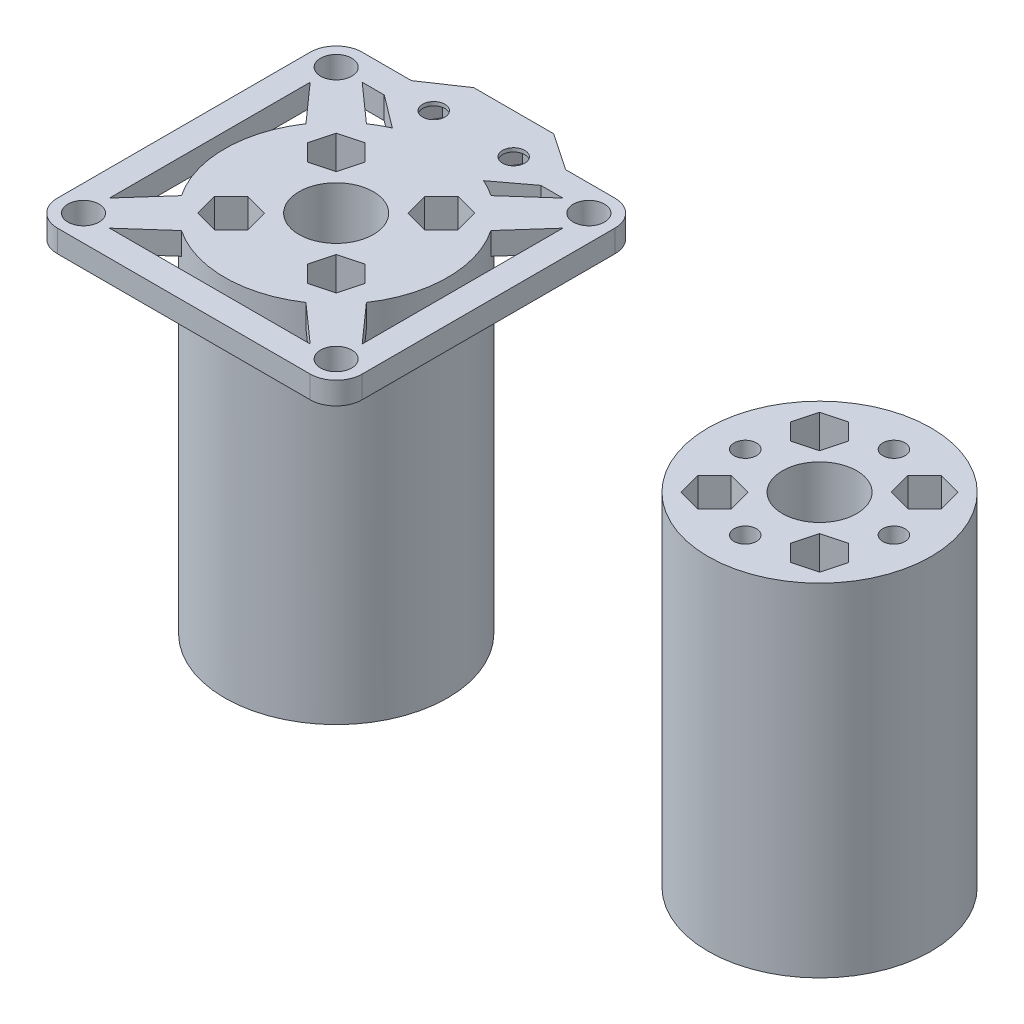
SolidWorks part; units mm, degrees
ref_plane "前视基准面" through (0, 0, 0) normal (0, 0, 1) x (1, 0, 0)
ref_plane "上视基准面" through (0, 0, 0) normal (0, 1, 0) x (1, 0, 0)
ref_plane "右视基准面" through (0, 0, 0) normal (1, 0, 0) x (0, 0, -1)
sketch "草图1" plane through (0, 0, 0) normal (0, 1, 0) x (1, 0, 0)
  circle A0 centre (-5.3729, -8.9317) radius 15
  circle A1 centre (-22.3729, 8.0683) radius 2.1
  circle A5 centre (-5.3729, -8.9317) radius 5
  circle A6 centre (-22.3729, 8.0683) radius 3.5
  dimension "D4" = 4.2
  dimension "D8" = 10
  dimension "D9" = 7
extrude "凸台-拉伸4" add sketch "草图1" along normal blind 3
sketch "草图5" plane through (0, 0, 0) normal (0, 1, 0) x (1, 0, 0)
  line L0 (-22.3729, 4.5683) -> (-10.3729, -8.9317)
  line L1 (-5.3729, -3.9317) -> (-18.8729, 8.0683)
  line L2 (-18.8729, 8.0683) -> (-22.3729, 4.5683)
  line L3 (-10.3729, -8.9317) -> (-10.3729, -3.9317)
  line L4 (-10.3729, -3.9317) -> (-5.3729, -3.9317)
  circle A0 centre (-22.3729, 8.0683) radius 3.5 construction
  circle A1 centre (-5.3729, -8.9317) radius 5 construction
extrude "凸台-拉伸5" add sketch "草图5" along normal blind 3
pattern_circular "阵列(圆周)2" count 4 over 360 about axis through (-5.3729, 0, 8.9317) along (0, 1, 0) of "凸台-拉伸5"
sketch "草图6" plane through (0, 3, 0) normal (0, 1, 0) x (1, 0, 0)
  circle A0 centre (11.6271, 8.0683) radius 2.1
  circle A1 centre (11.6271, 8.0683) radius 3.5
  dimension "D2" = 4.2
  dimension "D3" = 7
extrude "凸台-拉伸6" add sketch "草图6" against normal blind 3
pattern_circular "阵列(圆周)3" count 4 over 360 about axis through (-5.3729, 0, 8.9317) along (0, 1, 0) of "凸台-拉伸6"
sketch "草图7" plane through (0, 0, 0) normal (0, -1, 0) x (1, 0, 0)
  circle A0 centre (-5.3729, 8.9317) radius 15
  circle A1 centre (-5.3729, 8.9317) radius 5
extrude "凸台-拉伸7" add sketch "草图7" along normal blind 46
sketch "草图8" plane through (0, -46, 0) normal (0, -1, 0) x (1, 0, 0)
  line L4 (3.9435, 18.2482) -> (0.8763, 19.07)
  line L5 (0.8763, 19.07) -> (-1.3691, 16.8247)
  line L6 (-1.3691, 16.8247) -> (-0.5472, 13.7574)
  line L7 (-0.5472, 13.7574) -> (2.52, 12.9356)
  line L8 (2.52, 12.9356) -> (4.7654, 15.1809)
  line L9 (4.7654, 15.1809) -> (3.9435, 18.2482)
  circle A3 centre (1.6982, 16.0028) radius 2.75 construction
  dimension "D1" = 5.5
sketch "草图9" plane through (0, 3, 0) normal (0, 1, 0) x (1, 0, 0)
  line L0 (0.8763, -19.07) -> (-1.3691, -16.8247) construction
  line L1 (3.9435, -18.2482) -> (0.8763, -19.07) construction
  line L2 (4.7654, -15.1809) -> (3.9435, -18.2482) construction
  line L3 (2.52, -12.9356) -> (4.7654, -15.1809) construction
  line L4 (-0.5472, -13.7574) -> (2.52, -12.9356) construction
  line L5 (-1.3691, -16.8247) -> (-0.5472, -13.7574) construction
  line L6 (0.8763, -19.07) -> (-1.3691, -16.8247)
  line L7 (3.9435, -18.2482) -> (0.8763, -19.07)
  line L8 (4.7654, -15.1809) -> (3.9435, -18.2482)
  line L9 (2.52, -12.9356) -> (4.7654, -15.1809)
  line L10 (-0.5472, -13.7574) -> (2.52, -12.9356)
  line L11 (-1.3691, -16.8247) -> (-0.5472, -13.7574)
extrude "切除-拉伸1" cut sketch "草图9" against normal blind 46
pattern_circular "阵列(圆周)4" count 4 over 360 about axis through (-5.3729, 0, 8.9317) along (0, 1, 0) of "切除-拉伸1"
sketch "草图11" plane through (0, -43, 0) normal (0, 1, 0) x (1, 0, 0)
  circle A0 centre (1.6982, -1.8607) radius 1.5
  dimension "D1" = 3
extrude "切除-拉伸2" cut sketch "草图11" against normal blind 3
pattern_circular "阵列(圆周)5" count 4 over 360 about axis through (-5.3729, 0, 8.9317) along (0, 1, 0) of "切除-拉伸2"
sketch "草图12" plane through (0, 3, 0) normal (0, 1, 0) x (1, 0, 0)
  line L0 (15.1271, 8.0683) -> (15.1271, -25.9317)
  line L1 (15.1271, -25.9317) -> (11.6271, -22.4317)
  line L2 (11.6271, -22.4317) -> (11.6271, 4.5683)
  line L3 (11.6271, 4.5683) -> (15.1271, 8.0683)
  arc A0 (11.6271, 4.5683) -> (8.1271, 8.0683) centre (11.6271, 8.0683) ccw construction
  arc A1 (8.1271, -25.9317) -> (11.6271, -22.4317) centre (11.6271, -25.9317) ccw construction
extrude "凸台-拉伸8" add sketch "草图12" against normal blind 3
sketch "草图13" plane through (0, 3, 0) normal (0, 1, 0) x (1, 0, 0)
  line L0 (11.6271, 11.5683) -> (-22.3729, 11.5683)
  line L1 (-22.3729, 11.5683) -> (-18.8729, 8.0683)
  line L2 (-18.8729, 8.0683) -> (8.1271, 8.0683)
  line L3 (8.1271, 8.0683) -> (11.6271, 11.5683)
  arc A0 (15.1271, 8.0683) -> (8.1271, 8.0683) centre (11.6271, 8.0683) ccw construction
  arc A1 (-18.8729, 8.0683) -> (-22.3729, 4.5683) centre (-22.3729, 8.0683) ccw construction
extrude "凸台-拉伸9" add sketch "草图13" against normal blind 3
sketch "草图14" plane through (0, 3, 0) normal (0, 1, 0) x (1, 0, 0)
  line L0 (-25.8729, 8.0683) -> (-25.8729, -25.9317)
  line L1 (-25.8729, -25.9317) -> (-22.3729, -22.4317)
  line L2 (-22.3729, -22.4317) -> (-22.3729, 4.5683)
  line L3 (-22.3729, 4.5683) -> (-25.8729, 8.0683)
  arc A0 (-22.3729, 11.5683) -> (-22.3729, 4.5683) centre (-22.3729, 8.0683) ccw construction
  arc A1 (-22.3729, -22.4317) -> (-18.8729, -25.9317) centre (-22.3729, -25.9317) ccw construction
extrude "凸台-拉伸10" add sketch "草图14" against normal blind 3
sketch "草图15" plane through (0, 3, 0) normal (0, 1, 0) x (1, 0, 0)
  line L0 (-22.3729, -29.4317) -> (11.6271, -29.4317)
  line L1 (11.6271, -29.4317) -> (8.1271, -25.9317)
  line L2 (8.1271, -25.9317) -> (-18.8729, -25.9317)
  line L3 (-18.8729, -25.9317) -> (-22.3729, -29.4317)
  arc A0 (-25.8729, -25.9317) -> (-18.8729, -25.9317) centre (-22.3729, -25.9317) ccw construction
  arc A1 (8.1271, -25.9317) -> (15.1271, -25.9317) centre (11.6271, -25.9317) ccw construction
extrude "凸台-拉伸11" add sketch "草图15" against normal blind 3
sketch "草图16" plane through (0, 0, 0) normal (0, -1, 0) x (1, 0, 0)
  line L0 (-10.7479, -4.1933) -> (0.0021, -4.1933)
  line L1 (0.0021, -4.1933) -> (5.1636, -8.0683)
  line L2 (-18.8729, -8.0683) -> (8.1271, -8.0683) construction
  line L3 (4.9912, -11.5683) -> (0.0021, -14.9433)
  line L4 (11.6271, -11.5683) -> (-22.3729, -11.5683) construction
  line L5 (-7.5725, -9.5683) -> (-9.1602, -6.8183)
  line L6 (-9.1602, -6.8183) -> (-12.3356, -6.8183)
  line L7 (-12.3356, -6.8183) -> (-13.9233, -9.5683)
  line L8 (-13.9233, -9.5683) -> (-12.3356, -12.3183)
  line L9 (-12.3356, -12.3183) -> (-9.1602, -12.3183)
  line L10 (-9.1602, -12.3183) -> (-7.5725, -9.5683)
  line L11 (3.1775, -9.5683) -> (1.5898, -6.8183)
  line L12 (1.5898, -6.8183) -> (-1.5856, -6.8183)
  line L13 (-1.5856, -6.8183) -> (-3.1733, -9.5683)
  line L14 (-3.1733, -9.5683) -> (-1.5856, -12.3183)
  line L15 (-1.5856, -12.3183) -> (1.5898, -12.3183)
  line L16 (1.5898, -12.3183) -> (3.1775, -9.5683)
  line L17 (0.0021, -14.9433) -> (-10.7479, -14.9433)
  line L18 (-10.7479, -14.9433) -> (-15.7369, -11.5683)
  line L19 (-15.7369, -11.5683) -> (-15.9094, -8.0683)
  line L20 (-15.9094, -8.0683) -> (-10.7479, -4.1933)
  line L21 (4.9912, -11.5683) -> (5.1636, -8.0683)
  circle A0 centre (-10.7479, -9.5683) radius 2.75 construction
  circle A2 centre (0.0021, -9.5683) radius 2.75 construction
  dimension "D4" = 5.5
  dimension "D5" = 5.5
sketch "草图17" plane through (0, 0, 0) normal (0, -1, 0) x (1, 0, 0)
  line L1 (-7.5725, -9.5683) -> (-9.1602, -6.8183)
  line L2 (-9.1602, -6.8183) -> (-12.3356, -6.8183)
  line L3 (-12.3356, -6.8183) -> (-13.9233, -9.5683)
  line L4 (-13.9233, -9.5683) -> (-12.3356, -12.3183)
  line L5 (-12.3356, -12.3183) -> (-9.1602, -12.3183)
  line L6 (-9.1602, -12.3183) -> (-7.5725, -9.5683)
  line L7 (3.1775, -9.5683) -> (1.5898, -6.8183)
  line L8 (1.5898, -6.8183) -> (-1.5856, -6.8183)
  line L9 (-1.5856, -6.8183) -> (-3.1733, -9.5683)
  line L10 (-3.1733, -9.5683) -> (-1.5856, -12.3183)
  line L11 (-1.5856, -12.3183) -> (1.5898, -12.3183)
  line L12 (1.5898, -12.3183) -> (3.1775, -9.5683)
  circle A0 centre (-10.7479, -9.5683) radius 2.75 construction
  circle A1 centre (0.0021, -9.5683) radius 2.75 construction
extrude "凸台-拉伸13" add sketch "草图16" against normal blind 3
sketch "草图18" plane through (0, 0, 0) normal (0, -1, 0) x (1, 0, 0)
  line L1 (-7.5725, -9.5683) -> (-9.1602, -6.8183)
  line L2 (-9.1602, -6.8183) -> (-12.3356, -6.8183)
  line L3 (-12.3356, -6.8183) -> (-13.9233, -9.5683)
  line L4 (-13.9233, -9.5683) -> (-12.3356, -12.3183)
  line L5 (-12.3356, -12.3183) -> (-9.1602, -12.3183)
  line L6 (-9.1602, -12.3183) -> (-7.5725, -9.5683)
  line L7 (3.1775, -9.5683) -> (1.5898, -6.8183)
  line L8 (1.5898, -6.8183) -> (-1.5856, -6.8183)
  line L9 (-1.5856, -6.8183) -> (-3.1733, -9.5683)
  line L10 (-3.1733, -9.5683) -> (-1.5856, -12.3183)
  line L11 (-1.5856, -12.3183) -> (1.5898, -12.3183)
  line L12 (1.5898, -12.3183) -> (3.1775, -9.5683)
  circle A0 centre (-10.7479, -9.5683) radius 2.75 construction
  circle A1 centre (0.0021, -9.5683) radius 2.75 construction
extrude "凸台-拉伸14" add sketch "草图18" against normal blind 3
extrude "切除-拉伸3" cut sketch "草图17" against normal blind 2.5
sketch "草图19" plane through (0, 2.5, 0) normal (0, -1, 0) x (1, 0, 0)
  circle A0 centre (0.0021, -9.5683) radius 1.5
  dimension "D1" = 3
extrude "切除-拉伸4" cut sketch "草图19" against normal blind 2.5
sketch "草图20" plane through (0, 2.5, 0) normal (0, -1, 0) x (1, 0, 0)
  circle A0 centre (-10.7479, -9.5683) radius 1.5
  dimension "D1" = 3
extrude "切除-拉伸5" cut sketch "草图20" against normal blind 2.5
sketch "草图21" plane through (0, 0, 0) normal (0, 1, 0) x (1, 0, 0)
  circle A0 centre (59.6655, -8.9317) radius 15
  circle A1 centre (59.6655, -8.9317) radius 5
  dimension "D1" = 30
  dimension "D2" = 10
extrude "凸台-拉伸15" add sketch "草图21" along normal blind 3 separate body
sketch "草图22" plane through (0, 0, 0) normal (0, -1, 0) x (1, 0, 0)
  circle A0 centre (59.6655, 18.9317) radius 1.5
  dimension "D2" = 3
extrude "切除-拉伸6" cut sketch "草图22" against normal blind 3
pattern_circular "阵列(圆周)6" count 4 over 360 about axis through (59.6655, 0, 8.9317) along (0, 1, 0) of "切除-拉伸6"
extrude "凸台-拉伸16" add sketch "草图8" along normal blind 3
sketch "草图24" plane through (0, -49, 0) normal (0, -1, 0) x (1, 0, 0)
  line L1 (4.7654, 15.1809) -> (3.9435, 18.2482)
  line L2 (3.9435, 18.2482) -> (0.8763, 19.07)
  line L3 (0.8763, 19.07) -> (-1.3691, 16.8247)
  line L4 (-1.3691, 16.8247) -> (-0.5472, 13.7574)
  line L5 (-0.5472, 13.7574) -> (2.52, 12.9356)
  line L6 (2.52, 12.9356) -> (4.7654, 15.1809)
  circle A0 centre (1.6982, 16.0028) radius 2.75 construction
extrude "切除-拉伸7" cut sketch "草图24" against normal blind 3
sketch "草图25" plane through (0, 0, 0) normal (0, -1, 0) x (1, 0, 0)
  circle A0 centre (59.6655, 8.9317) radius 15
  circle A1 centre (59.6655, 8.9317) radius 5
extrude "凸台-拉伸17" add sketch "草图25" along normal blind 43
sketch "草图27" plane through (0, 3, 0) normal (0, 1, 0) x (1, 0, 0)
  circle A0 centre (59.6655, 1.0683) radius 1.5
  circle A1 centre (69.6655, -8.9317) radius 1.5
  circle A2 centre (59.6655, -18.9317) radius 1.5
  circle A3 centre (49.6655, -8.9317) radius 1.5
extrude "切除-拉伸8" cut sketch "草图27" against normal blind 46
sketch "草图28" plane through (0, -43, 0) normal (0, -1, 0) x (1, 0, 0)
  circle A0 centre (59.6655, 18.9317) radius 2.75
  circle A1 centre (49.6655, 8.9317) radius 2.75
  circle A2 centre (59.6655, -1.0683) radius 2.75
  circle A3 centre (69.6655, 8.9317) radius 2.75
  dimension "D1" = 5.5
  dimension "D2" = 5.5
  dimension "D3" = 5.5
  dimension "D4" = 5.5
extrude "切除-拉伸9" cut sketch "草图28" against normal blind 43
sketch "草图29" plane through (0, 3, 0) normal (0, 1, 0) x (1, 0, 0)
  circle A0 centre (66.7366, -1.8607) radius 1.5
  dimension "D2" = 3
extrude "切除-拉伸10" cut sketch "草图29" against normal blind 46
pattern_circular "阵列(圆周)7" count 4 over 360 about axis through (59.6655, 0, 8.9317) along (0, 1, 0) of "切除-拉伸10"
sketch "草图30" plane through (0, 3, 0) normal (0, 1, 0) x (1, 0, 0)
  line L2 (64.4912, -4.106) -> (67.5585, -4.9279)
  line L3 (67.5585, -4.9279) -> (69.8038, -2.6825)
  line L4 (69.8038, -2.6825) -> (68.982, 0.3847)
  line L5 (68.982, 0.3847) -> (65.9148, 1.2066)
  line L6 (65.9148, 1.2066) -> (63.6694, -1.0388)
  line L7 (63.6694, -1.0388) -> (64.4912, -4.106)
  circle A0 centre (66.7366, -1.8607) radius 2.75 construction
  dimension "D1" = 5.5
extrude "切除-拉伸11" cut sketch "草图30" against normal blind 43
pattern_circular "阵列(圆周)8" count 4 over 360 about axis through (59.6655, 0, 8.9317) along (0, 1, 0) of "切除-拉伸11"
